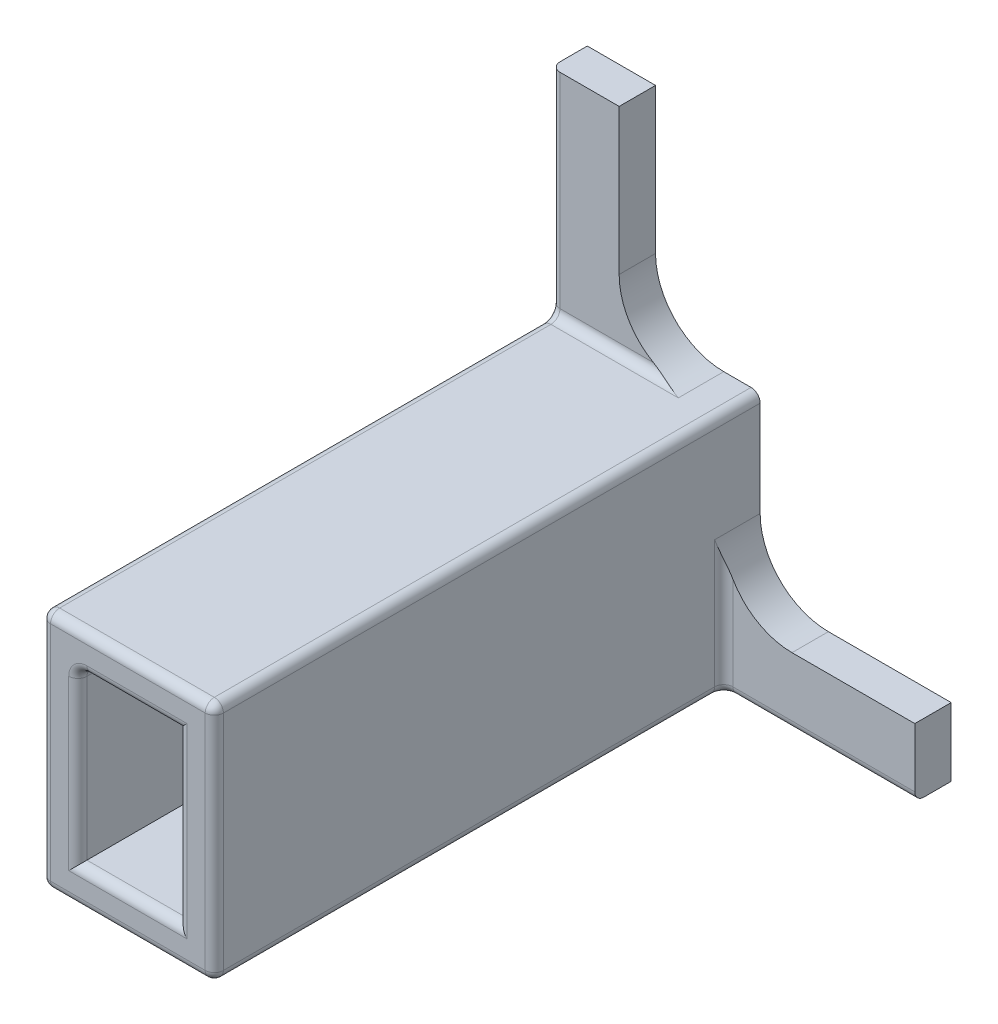
SolidWorks part; units mm, degrees
ref_plane "Płaszczyzna przednia" through (0, 0, 0) normal (0, 0, 1) x (1, 0, 0)
ref_plane "Płaszczyzna górna" through (0, 0, 0) normal (0, 1, 0) x (1, 0, 0)
ref_plane "Płaszczyzna prawa" through (0, 0, 0) normal (1, 0, 0) x (0, 0, -1)
sketch "Szkic1" plane through (0, 0, 0) normal (0, 0, 1) x (1, 0, 0)
  line L0 (0, 0) -> (0, 100)
  line L1 (0, 100) -> (15, 100)
  line L2 (15, 100) -> (15, 53)
  line L3 (15, 53) -> (38, 53)
  line L4 (80, 15) -> (80, 0)
  line L5 (80, 0) -> (0, 0)
  line L6 (38, 53) -> (38, 15)
  line L7 (8, 8) -> (30, 8)
  line L8 (8, 8) -> (8, 45)
  line L9 (8, 45) -> (30, 45)
  line L10 (30, 8) -> (30, 45)
  line L11 (38, 15) -> (80, 15)
  dimension "D1" = 80
  dimension "D2" = 100
  dimension "D3" = 15
  dimension "D4" = 22
  dimension "D5" = 37
  dimension "D6" = 8
  dimension "D7" = 8
  dimension "D8" = 8
  dimension "D9" = 15
  dimension "D10" = 8
extrude "Dodanie-wyciągnięcie1" add sketch "Szkic1" along normal blind 120
sketch "Szkic2" plane through (0, 0, 120) normal (0, 0, 1) x (1, 0, 0)
  line L0 (0, 0) -> (80, 0) construction
  line L1 (80, 15) -> (38, 15)
  line L2 (80, 15) -> (80, 0)
  line L3 (80, 0) -> (38, 0)
  line L4 (38, 15) -> (38, 0)
  line L5 (0, 100) -> (0, 0) construction
  line L6 (15, 100) -> (0, 100)
  line L7 (15, 100) -> (15, 53)
  line L8 (15, 53) -> (0, 53)
  line L9 (0, 100) -> (0, 53)
  line L10 (38, 53) -> (15, 53) construction
  line L11 (38, 15) -> (38, 53) construction
extrude "Wytnij-wyciągnięcie1" cut sketch "Szkic2" against normal offset from surface (112 mm away) 8 up to face at (33.25, 42, 0)
fillet "Zaokrąglenie1" radius 15 2 edges at (38, 15, 4) (15, 53, 4)
fillet "Zaokrąglenie2" radius 2 17 edges at (19, 8, 120) (30, 26.5, 120) (19, 45, 120) (8, 26.5, 120) (38, 26.5, 120) (38, 15, 8) (19, 0, 120) (38, 0, 64) (59, 0, 8) (0, 26.5, 120) (0, 0, 60) (0, 76.5, 8) (38, 53, 60) (19, 53, 120) (0, 53, 64) (15, 53, 8) (8, 45, 60)
